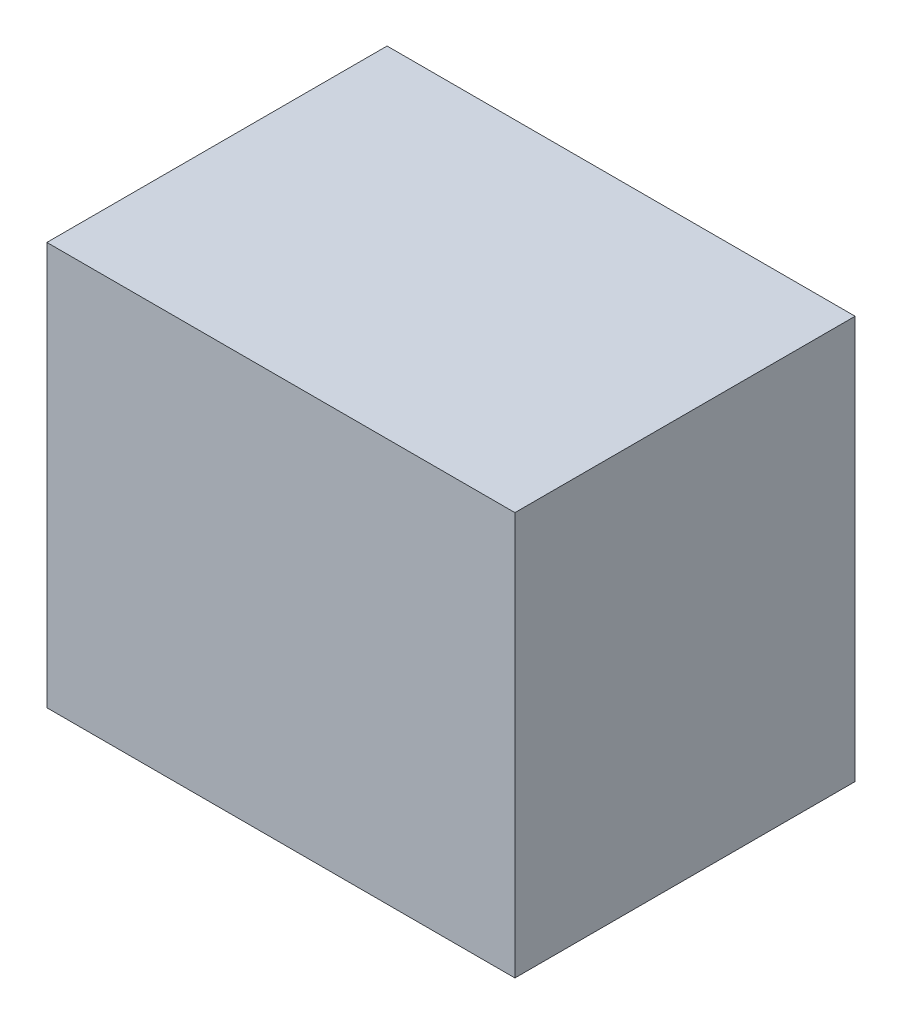
SolidWorks part; units mm, degrees
ref_plane "Front Plane" through (0, 0, 0) normal (0, 0, 1) x (1, 0, 0)
ref_plane "Top Plane" through (0, 0, 0) normal (0, 1, 0) x (1, 0, 0)
ref_plane "Right Plane" through (0, 0, 0) normal (1, 0, 0) x (0, 0, -1)
sketch "Sketch1" plane through (0, 0, 0) normal (0, 1, 0) x (1, 0, 0)
  line L1 (0, 0) -> (54, 0)
  line L2 (0, 0) -> (0, 39.25)
  line L3 (0, 39.25) -> (54, 39.25)
  line L4 (54, 0) -> (54, 39.25)
  dimension "D1" = 54
  dimension "D2" = 39.25
extrude "Boss-Extrude1" add sketch "Sketch1" along normal blind 46.5
